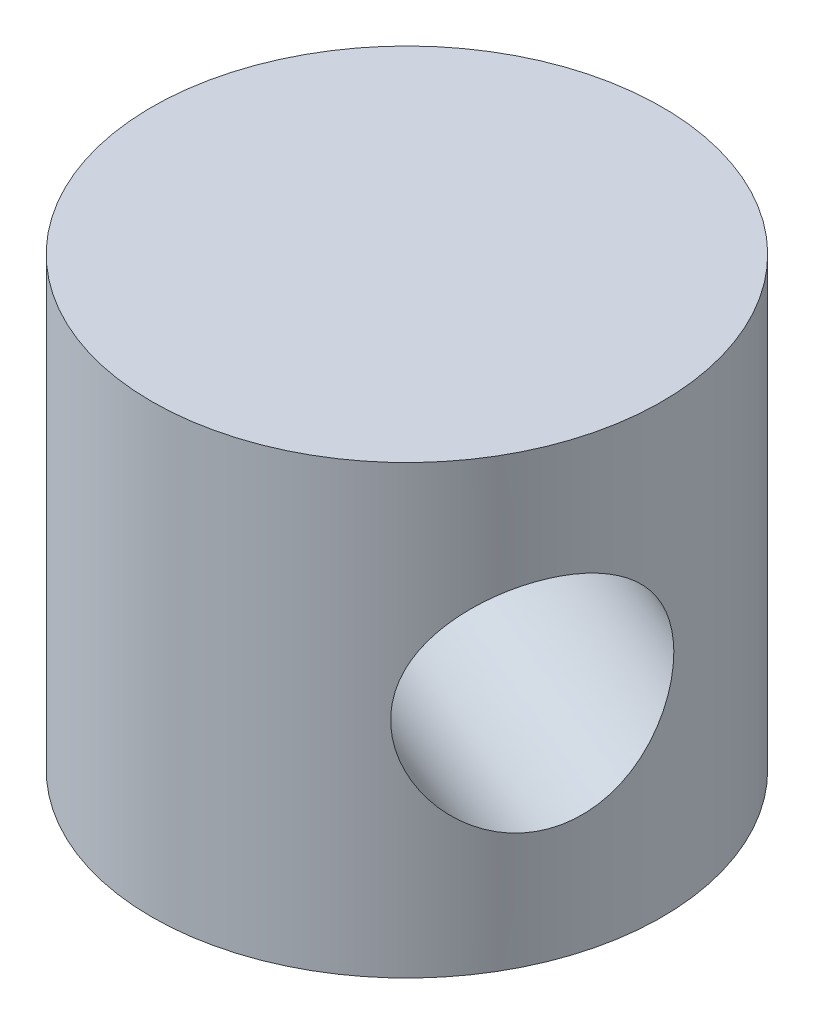
SolidWorks part; units mm, degrees
material "2.0402 (CuZn40Pb2)"
ref_plane "Front Plane" through (0, 0, 0) normal (0, 0, 1) x (1, 0, 0)
ref_plane "Top Plane" through (0, 0, 0) normal (0, 1, 0) x (1, 0, 0)
ref_plane "Right Plane" through (0, 0, 0) normal (1, 0, 0) x (0, 0, -1)
sketch "Sketch1" plane through (0, 0, 0) normal (0, 1, 0) x (1, 0, 0)
  circle A0 centre (0, 0) radius 8
extrude "Boss-Extrude1" add sketch "Sketch1" along normal blind 14
hole_wizard "M8 Tapped Hole1" positions "3DSketch1" profile "Sketch2" tap size "M8" standard "DIN" end condition through all
sketch3d "3DSketch1"
  point P0 (7.394, 7, 3.0542)
  dimension "D1" = 7
sketch "Sketch2" plane through (7.394, 7, 3.0542) normal (0, 1, 0) x (0.3818, 0, -0.9243)
  line L0 (0, 0) -> (0, 18.4482)
  line L1 (0, 18.4482) -> (3.4, 18.4482)
  line L2 (3.4, 18.4482) -> (3.4, 0)
  line L5 (3.4, 0) -> (0, 0)
  line L11 (0, -6.35) -> (0, 107.95) construction
  dimension "Thru Tap Drill Dia." = 6.8
  dimension "Thru Tap Drill Depth" = 18.4482
cosmetic thread "Hole Thread1"
